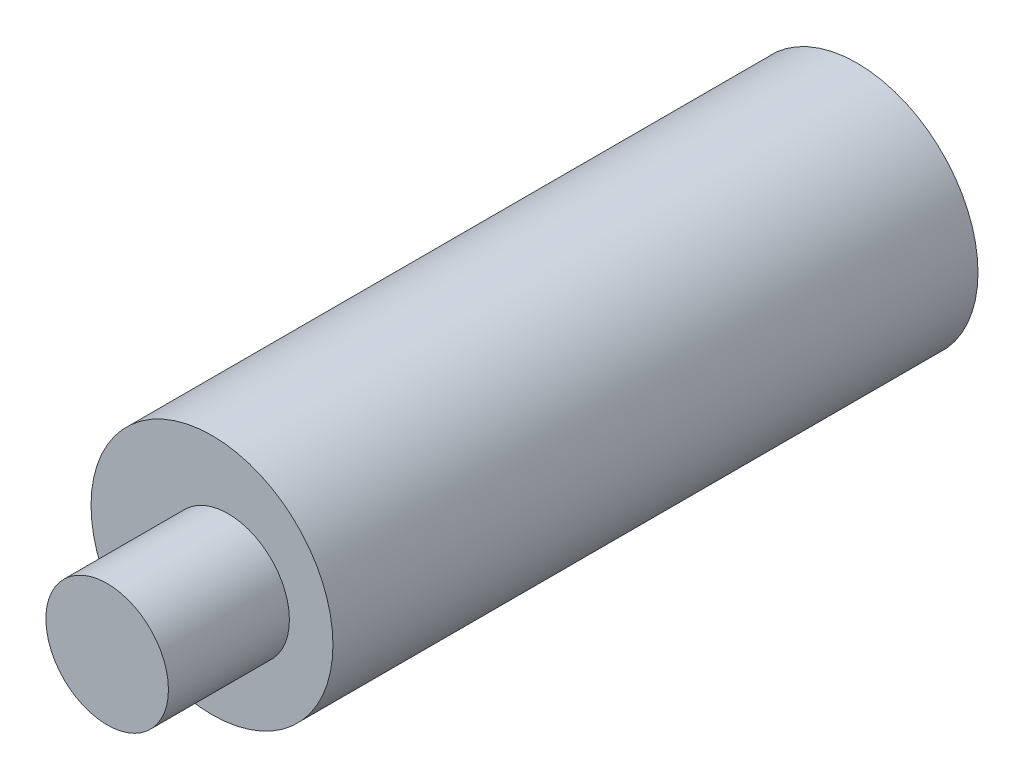
SolidWorks part; units mm, degrees
ref_plane "Front" through (0, 0, 0) normal (0, 0, 1) x (1, 0, 0)
ref_plane "Top" through (0, 0, 0) normal (0, 1, 0) x (1, 0, 0)
ref_plane "Right" through (0, 0, 0) normal (1, 0, 0) x (0, 0, -1)
sketch "Sketch1" plane through (0, 0, 0) normal (0, 0, 1) x (1, 0, 0)
  circle A0 centre (0, 0) radius 4.7625
  dimension "D1" = 9.525
extrude "Boss-Extrude2" add sketch "Sketch1" along normal blind 25.4
sketch "Sketch4" plane through (0, 0, 25.4) normal (0, 0, 1) x (1, 0, 0)
  line L0 (0.635, 0) -> (0, 0) construction
  circle A0 centre (0.635, 0) radius 2.413
  dimension "D1" = 4.826
  dimension "D2" = 0.635
extrude "Boss-Extrude3" add sketch "Sketch4" along normal blind 4.7625
sketch "Sketch5" plane through (0, 0, 0) normal (0, 0, -1) x (-1, 0, 0)
  circle A0 centre (0, 0) radius 2.5527
  dimension "D1" = 5.1054
extrude "Cut-Extrude2" cut sketch "Sketch5" against normal blind 19.05
